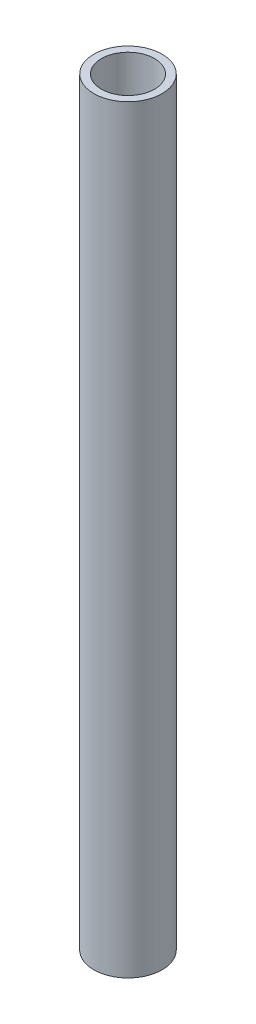
SolidWorks part; units mm, degrees
material "Acier non allié"
ref_plane "Plan de face" through (0, 0, 0) normal (0, 0, 1) x (1, 0, 0)
ref_plane "Plan de dessus" through (0, 0, 0) normal (0, 1, 0) x (1, 0, 0)
ref_plane "Plan de droite" through (0, 0, 0) normal (1, 0, 0) x (0, 0, -1)
sketch "Esquisse1" plane through (0, 0, 0) normal (0, 1, 0) x (1, 0, 0)
  circle A0 centre (0, 0) radius 9
  circle A1 centre (0, 0) radius 7
  dimension "D1" = 18
  dimension "D2" = 14
  dimension "D3" = 2
extrude "Boss.-Extru.1" add sketch "Esquisse1" along normal blind 200
